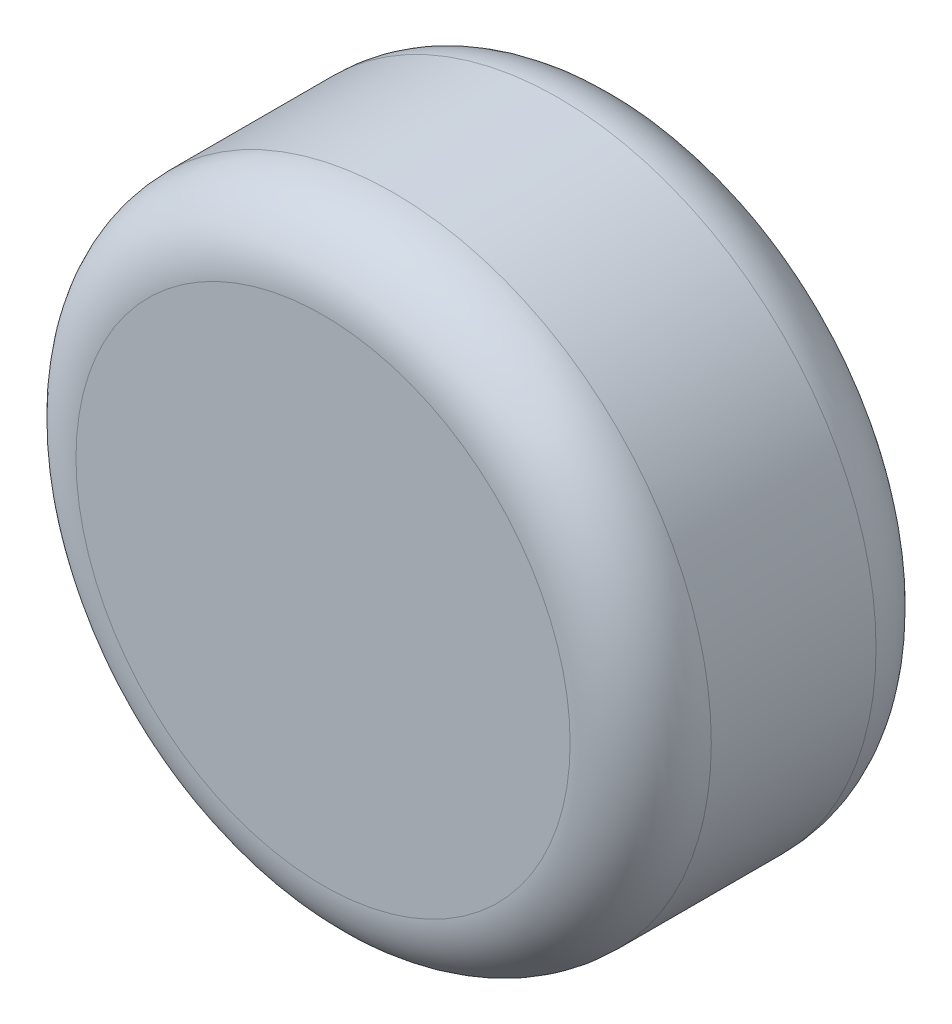
SolidWorks part; units mm, degrees
ref_plane "Plan de face" through (0, 0, 0) normal (0, 0, 1) x (1, 0, 0)
ref_plane "Plan de dessus" through (0, 0, 0) normal (0, 1, 0) x (1, 0, 0)
ref_plane "Plan de droite" through (0, 0, 0) normal (1, 0, 0) x (0, 0, -1)
sketch "Esquisse1" plane through (0, 0, 0) normal (0, 0, 1) x (1, 0, 0)
  circle A0 centre (0, 0) radius 67.5
  dimension "D1" = 135
extrude "Boss.-Extru.1" add sketch "Esquisse1" along normal blind 65
fillet "Congé1" radius 15 2 edges at (67.5, 0, 0) (67.5, 0, 65)
